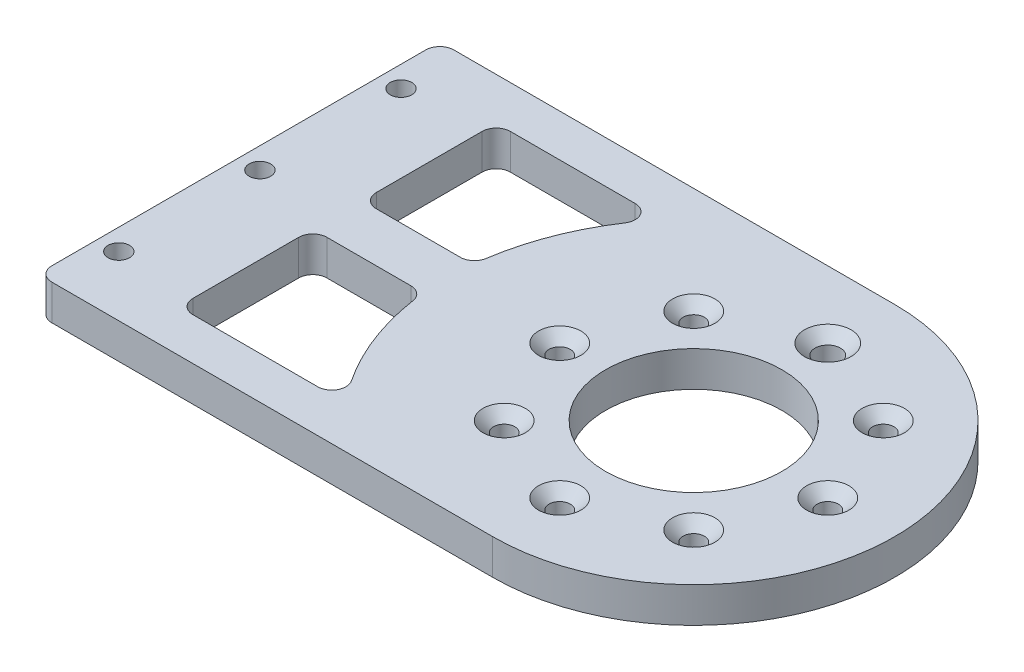
SolidWorks part; units mm, degrees
material "Thornel Mat VMA"
ref_plane "前视基准面" through (0, 0, 0) normal (0, 0, 1) x (1, 0, 0)
ref_plane "上视基准面" through (0, 0, 0) normal (0, 1, 0) x (1, 0, 0)
ref_plane "右视基准面" through (0, 0, 0) normal (1, 0, 0) x (0, 0, -1)
other "Configuration Table"
sketch "草图1" plane through (0, 0, 0) normal (0, 1, 0) x (1, 0, 0)
  line L1 (-105, -28.5) -> (105, -28.5)
  line L2 (-105, -28.5) -> (-105, 28.5) construction
  line L3 (-105, 28.5) -> (105, 28.5)
  line L4 (105, -28.5) -> (105, 28.5)
  line L5 (-105, -28.5) -> (105, 28.5) construction
  line L6 (-105, 28.5) -> (105, -28.5) construction
  circle A0 centre (105, 0) radius 28.5
  circle A1 centre (-105, 0) radius 37
  point P0 (0, 0)
  dimension "D1" = 57
  dimension "D3" = 74
  dimension "D2" = 210
extrude "凸台-拉伸1" add sketch "草图1" along normal blind 5
sketch "草图2" plane through (0, 0, 0) normal (0, -1, 0) x (1, 0, 0)
  line L0 (118.435, 13.435) -> (105, 0) construction
  line L1 (105, 0) -> (133.5, 0) construction
  circle A0 centre (105, 0) radius 19 construction
  circle A1 centre (118.435, 13.435) radius 1.275
  arc A2 (105, -28.5) -> (105, 28.5) centre (105, 0) ccw construction
  circle A3 centre (118.435, -13.435) radius 1.275
  circle A4 centre (91.565, -13.435) radius 1.275
  circle A5 centre (91.565, 13.435) radius 1.275
  circle A6 centre (124, 0) radius 1.275
  circle A7 centre (105, -19) radius 1.275
  circle A8 centre (86, 0) radius 1.275
  circle A9 centre (105, 19) radius 1.275
  point P18 (105, 0)
  point P26 (105, 0)
  dimension "D1" = 38
  dimension "D3" = 2.55
  dimension "D4" = 4
  dimension "D2" = 45
  dimension "D5" = 4
extrude "切除-拉伸1" cut sketch "草图2" against normal through all
sketch "草图3" plane through (0, 5, 0) normal (0, 1, 0) x (1, 0, 0)
  circle A16 centre (-105, 0) radius 17.25 construction
  circle A17 centre (-105, 17.25) radius 2.025
  circle A18 centre (-90.0611, 8.625) radius 2.025
  circle A19 centre (-90.0611, -8.625) radius 2.025
  circle A20 centre (-105, -17.25) radius 2.025
  circle A21 centre (-119.9389, -8.625) radius 2.025
  circle A22 centre (-119.9389, 8.625) radius 2.025
  point P18 (-105, 0)
  dimension "D1" = 34.5
  dimension "D2" = 4.05
sketch "草图5" plane through (0, 5, 0) normal (0, 1, 0) x (1, 0, 0)
  circle A0 centre (-105, 0) radius 10
  dimension "D1" = 20
extrude "切除-拉伸3" cut sketch "草图5" against normal through all
sketch "草图6" plane through (0, 5, 0) normal (0, 1, 0) x (1, 0, 0)
  circle A0 centre (-105, 0) radius 30 construction
  circle A1 centre (-135, 0) radius 1.525
  circle A2 centre (-120, 25.9808) radius 1.525
  circle A3 centre (-90, 25.9808) radius 1.525
  circle A4 centre (-75, 0) radius 1.525
  circle A5 centre (-90, -25.9808) radius 1.525
  circle A6 centre (-120, -25.9808) radius 1.525
  point P17 (-105, 0)
  dimension "D1" = 60
  dimension "D2" = 3.05
  dimension "D3" = 6
extrude "切除-拉伸4" cut sketch "草图6" against normal through all
sketch "草图7" plane through (0, 5, 0) normal (0, 1, 0) x (1, 0, 0)
  line L0 (-81.4044, 28.5) -> (105, 28.5) construction
  line L1 (0, 0) -> (50000, 0) construction
  circle A0 centre (-60, 23.5) radius 1.525
  circle A1 centre (-27, 23.5) radius 1.525
  circle A2 centre (6, 23.5) radius 1.525
  circle A3 centre (39, 23.5) radius 1.525
  circle A4 centre (72, 23.5) radius 1.525
  circle A5 centre (72, -23.5) radius 1.525
  circle A6 centre (39, -23.5) radius 1.525
  circle A7 centre (6, -23.5) radius 1.525
  circle A8 centre (-27, -23.5) radius 1.525
  circle A9 centre (-60, -23.5) radius 1.525
  dimension "D1" = 3.05
  dimension "D2" = 5
  dimension "D3" = 60
  dimension "D5" = 33
  dimension "D4" = 5
sketch "草图8" plane through (0, 0, 0) normal (0, -1, 0) x (1, 0, 0)
  line L0 (-44.8493, 17.0002) -> (-34.9998, 17.0002) construction
  line L1 (-32.9998, -3.6043) -> (-32.9998, 15.0002) construction
  line L2 (-46.6169, 14.0644) -> (-36.7674, -4.5401) construction
  line L3 (-48.9998, -16.9998) -> (-39.1504, -16.9998) construction
  line L5 (-47.2323, 4.5405) -> (-37.3828, -14.064) construction
  line L6 (-50.9998, -14.9998) -> (-50.9998, 3.6047) construction
  line L7 (-44.8493, 17.0002) -> (-34.9998, 17.0002)
  line L13 (-32.9998, -3.6043) -> (-32.9998, 15.0002)
  line L14 (-46.6169, 14.0644) -> (-36.7674, -4.5401)
  line L15 (-48.9998, -16.9998) -> (-39.1504, -16.9998)
  line L21 (-47.2323, 4.5405) -> (-37.3828, -14.064)
  line L22 (-50.9998, -14.9998) -> (-50.9998, 3.6047)
  arc A0 (-44.8493, 17.0002) -> (-46.6169, 14.0644) centre (-44.8493, 15.0002) ccw construction
  arc A1 (-32.9998, 15.0002) -> (-34.9998, 17.0002) centre (-34.9998, 15.0002) ccw construction
  arc A2 (-36.7674, -4.5401) -> (-32.9998, -3.6043) centre (-34.9998, -3.6043) ccw construction
  arc A3 (-39.1504, -16.9998) -> (-37.3828, -14.064) centre (-39.1504, -14.9998) ccw construction
  arc A36 (-50.9998, -14.9998) -> (-48.9998, -16.9998) centre (-48.9998, -14.9998) ccw construction
  arc A37 (-47.2323, 4.5405) -> (-50.9998, 3.6047) centre (-48.9998, 3.6047) ccw construction
  arc A38 (-44.8493, 17.0002) -> (-46.6169, 14.0644) centre (-44.8493, 15.0002) ccw
  arc A39 (-32.9998, 15.0002) -> (-34.9998, 17.0002) centre (-34.9998, 15.0002) ccw
  arc A40 (-36.7674, -4.5401) -> (-32.9998, -3.6043) centre (-34.9998, -3.6043) ccw
  arc A41 (-39.1504, -16.9998) -> (-37.3828, -14.064) centre (-39.1504, -14.9998) ccw
  arc A42 (-50.9998, -14.9998) -> (-48.9998, -16.9998) centre (-48.9998, -14.9998) ccw
  arc A43 (-47.2323, 4.5405) -> (-50.9998, 3.6047) centre (-48.9998, 3.6047) ccw
sketch "草图9" plane through (0, 0, 0) normal (0, -1, 0) x (1, 0, 0)
  circle A0 centre (105, 0) radius 12.5
  dimension "D1" = 25
extrude "切除-拉伸7" cut sketch "草图9" against normal through all
hole_wizard "M3 十字槽沉头木螺钉的锥形沉头孔1" positions "草图10" profile "草图11" countersink size "M3" standard "GB" end condition through all
sketch "草图10" plane through (0, 5, 0) normal (0, 1, 0) x (1, 0, 0)
  point P0 (105, 19)
sketch "草图11" plane through (105, 5, -19) normal (1, 0, 0) x (0, 0, 1)
  line L0 (0, 0) -> (0, 5)
  line L1 (0, 5) -> (1.8, 5)
  line L2 (1.8, 5) -> (1.8, 1.5)
  line L3 (1.8, 1.5) -> (3.3, 0)
  line L5 (3.3, 0) -> (0, 0)
  line L6 (-1.8, 1.5) -> (-3.3, 0) construction
  line L11 (0, -6.35) -> (0, 107.95) construction
  dimension "通孔孔直径" = 3.6
  dimension "通孔孔深度" = 5
  dimension "近端锥形沉头孔直径" = 6.6
  dimension "近端锥形沉头孔角度" = 90
hole_wizard "孔1" positions "草图12" profile "草图13" legacy end condition through all
sketch "草图12" plane through (0, 5, 0) normal (0, 1, 0) x (1, 0, 0)
  point P0 (91.565, 13.435)
  point P3 (86, 0)
  point P6 (91.565, -13.435)
  point P9 (105, -19)
  point P12 (118.435, -13.435)
  point P15 (124, 0)
  point P18 (118.435, 13.435)
sketch "草图13" plane through (91.565, 5, -13.435) normal (1, 0, 0) x (0, 0, 1)
  line L0 (0, 0) -> (0, 5)
  line L1 (0, 5) -> (1.5, 5)
  line L2 (1.5, 5) -> (1.5, 1.5)
  line L3 (1.5, 1.5) -> (3, 0)
  line L4 (3, 0) -> (0, 0)
  line L5 (0, -6.4453) -> (0, 115.525) construction
  line L6 (-1.5, 1.5) -> (-3, 0) construction
  dimension "直径" = 3
  dimension "深度" = 5
  dimension "锥坑角度" = 90
  dimension "锥坑直径" = 6
extrude "切除-拉伸8" cut sketch "草图3" against normal blind 10
sketch "草图14" plane through (0, 5, 0) normal (0, 1, 0) x (1, 0, 0)
  circle A0 centre (-105, 0) radius 37
  arc A1 (-81.4044, 28.5) -> (-81.4044, -28.5) centre (-105, 0) ccw construction
extrude "凸台-拉伸2" add sketch "草图14" against normal up to surface (5 mm away) up to face at (-105, 0, -15.225)
sketch "草图15" plane through (0, 5, 0) normal (0, 1, 0) x (1, 0, 0)
  circle A0 centre (-105, 0) radius 42.5
  dimension "D1" = 85
extrude "凸台-拉伸3" add sketch "草图15" against normal up to surface (5 mm away) up to face at (91.565, 0, -11.935)
sketch "草图16" plane through (0, 0, 0) normal (0, -1, 0) x (1, 0, 0)
  circle A0 centre (-105, 0) radius 26.25 construction
  circle A1 centre (-105, 26.25) radius 2.025
  circle A2 centre (-86.4384, 18.5616) radius 2.025
  circle A3 centre (-78.75, 0) radius 2.025
  circle A4 centre (-86.4384, -18.5616) radius 2.025
  circle A5 centre (-105, -26.25) radius 2.025
  circle A6 centre (-123.5616, -18.5616) radius 2.025
  circle A7 centre (-131.25, 0) radius 2.025
  circle A8 centre (-123.5616, 18.5616) radius 2.025
  point P22 (-105, 0)
  dimension "D1" = 52.5
  dimension "D2" = 4.05
  dimension "D3" = 8
extrude "切除-拉伸9" cut sketch "草图16" against normal up to surface (5 mm away) up to face at (4.3819, 5, 0)
sketch "草图18" plane through (0, 5, 0) normal (0, 1, 0) x (1, 0, 0)
  line L0 (-98.8153, 17.25) -> (-101.4581, 12.1732)
  line L1 (-111.1847, 17.25) -> (-108.5419, 12.1732)
  line L2 (-105, 0) -> (-105, -17.25) construction
  circle A0 centre (-105, 0) radius 17.25 construction
  circle A1 centre (-105, 17.25) radius 3.8 construction
  circle A2 centre (-90.0611, 8.625) radius 3.8 construction
  circle A3 centre (-90.0611, -8.625) radius 3.8 construction
  circle A4 centre (-105, -17.25) radius 3.8 construction
  circle A5 centre (-119.9389, -8.625) radius 3.8 construction
  circle A6 centre (-119.9389, 8.625) radius 3.8 construction
  arc A7 (-111.1847, 17.25) -> (-98.8153, 17.25) centre (-105, 15.25) cw
  arc A8 (-108.5419, 12.1732) -> (-101.4581, 12.1732) centre (-105, 5) cw
  point P17 (-105, 0)
  dimension "D1" = 34.5
  dimension "D2" = 7.6
  dimension "D5" = 6.5
  dimension "D7" = 8
  dimension "D4" = 2
  dimension "D6" = 5
  dimension "D8" = 55
  dimension "D3" = 6
extrude "切除-拉伸10" cut sketch "草图18" against normal up to surface (5 mm away) up to face at (-105, 0, 24.225)
pattern_circular "阵列(圆周)1" count 6 over 360 about axis through (-105, 0, 0) along (0, 1, 0) of "切除-拉伸10"
sketch "草图19" plane through (0, 0, 0) normal (0, -1, 0) x (1, 0, 0)
  circle A0 centre (-105, 0) radius 6
  dimension "D1" = 12
extrude "切除-拉伸11" cut sketch "草图19" against normal up to surface (5 mm away) up to face at (-91.1061, 5, -8.0217)
sketch "草图20" plane through (0, 0, 0) normal (0, -1, 0) x (1, 0, 0)
  circle A10 centre (-105, 0) radius 36.75 construction
  circle A11 centre (-68.25, 0) radius 1.525
  circle A12 centre (-79.0138, -25.9862) radius 1.525
  circle A13 centre (-105, -36.75) radius 1.525
  circle A14 centre (-130.9862, -25.9862) radius 1.525
  circle A15 centre (-141.75, 0) radius 1.525
  circle A16 centre (-130.9862, 25.9862) radius 1.525
  circle A17 centre (-105, 36.75) radius 1.525
  circle A18 centre (-79.0138, 25.9862) radius 1.525
  point P21 (-105, 0)
  dimension "D1" = 73.5
  dimension "D2" = 3.05
fillet "圆角1" radius 2 2 edges at (-73.4722, 2.5, -28.5) (-73.4722, 2.5, 28.5)
sketch "草图21" plane through (0, 0, 0) normal (0, -1, 0) x (1, 0, 0)
  line L0 (-200000, 0) -> (250000, 0) construction
  line L1 (-148.9163, 68.8697) -> (40.5, 68.8697)
  line L2 (-148.9163, 68.8697) -> (-148.9163, -71.4241)
  line L3 (-148.9163, -71.4241) -> (40.5, -71.4241)
  line L4 (40.5, 68.8697) -> (40.5, -71.4241)
  circle A0 centre (105, 0) radius 12.5 construction
  dimension "D1" = 64.5
  dimension "D2" = 140.2938
  dimension "D3" = 68.8697
  dimension "D4" = 189.4163
extrude "切除-拉伸12" cut sketch "草图21" against normal through all
sketch "草图25" plane through (0, 0, 0) normal (0, -1, 0) x (1, 0, 0)
  line L0 (43.5, 28.5) -> (43.5, 50028.5) construction
  line L2 (40.5, -28.5) -> (40.5, 28.5) construction
  line L3 (0, 0) -> (43.5, 0) construction
  circle A0 centre (43.5, 0) radius 1.525
  circle A1 centre (43.5, 20) radius 1.525
  circle A2 centre (43.5, -20) radius 1.525
  dimension "D2" = 3.05
  dimension "D1" = 3
  dimension "D3" = 20
extrude "切除-拉伸13" cut sketch "草图25" against normal through all
fillet "圆角2" radius 2 2 edges at (40.5, 2.5, -28.5) (40.5, 2.5, 28.5)
sketch "草图28" plane through (0, 0, 0) normal (0, -1, 0) x (1, 0, 0)
  line L0 (40.5, -26.5) -> (40.5, 26.5) construction
  line L1 (54.5, -22.5) -> (78.1905, -22.5)
  line L2 (54.5, -22.5) -> (54.5, 22.5)
  line L3 (54.5, 22.5) -> (78.1905, 22.5)
  line L4 (78.1905, -22.5) -> (78.1905, 22.5)
  line L5 (54.5, -22.5) -> (78.1905, 22.5) construction
  line L6 (54.5, 22.5) -> (78.1905, -22.5) construction
  line L7 (54.5, 0) -> (78.1905, 0)
  line L8 (54.5, -3.5) -> (78.1905, -3.5)
  line L9 (54.5, 3.5) -> (78.1905, 3.5)
  circle A0 centre (105, 0) radius 35
  point P3 (66.3452, 0)
  dimension "D1" = 70
  dimension "D2" = 14
  dimension "D3" = 45
  dimension "D4" = 3.5
  dimension "D5" = 3.5
extrude "切除-拉伸14" cut sketch "草图28" against normal through all contours A0 L3 L2 L9 | A0 L8 L2 L1
fillet "圆角3" radius 2 8 edges at (54.5, 2.5, 3.5) (78.1905, 2.5, 22.5) (70.1754, 2.5, 3.5) (54.5, 2.5, -22.5) (54.5, 2.5, -3.5) (70.1754, 2.5, -3.5) (78.1905, 2.5, -22.5) (54.5, 2.5, 22.5)
